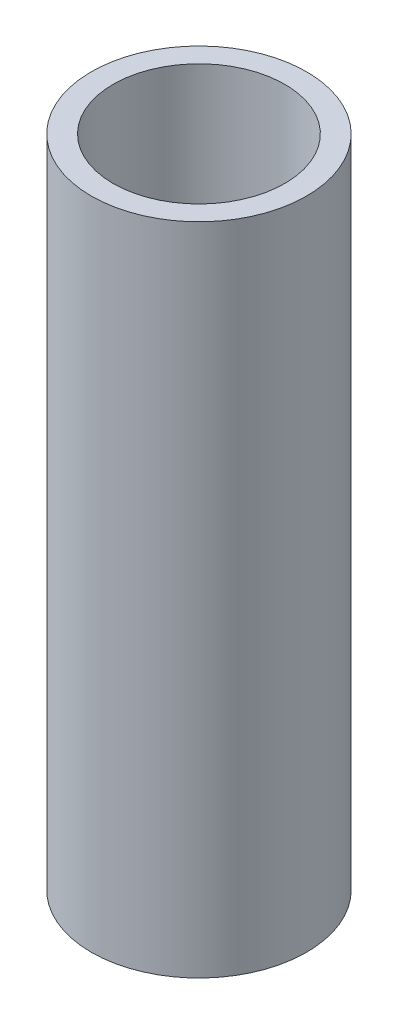
SolidWorks part; units mm, degrees
material "PVC Rigid"
ref_plane "Front" through (0, 0, 0) normal (0, 0, 1) x (1, 0, 0)
ref_plane "Top" through (0, 0, 0) normal (0, 1, 0) x (1, 0, 0)
ref_plane "Right" through (0, 0, 0) normal (1, 0, 0) x (0, 0, -1)
sketch "Sketch1" plane through (0, 0, 0) normal (0, 1, 0) x (1, 0, 0)
  circle A0 centre (0, 0) radius 16.7005
  circle A1 centre (0, 0) radius 13.3223
  dimension "D1" = 26.6446
  dimension "D2" = 33.401
extrude "Boss-Extrude1" add sketch "Sketch1" along normal blind 101.6
